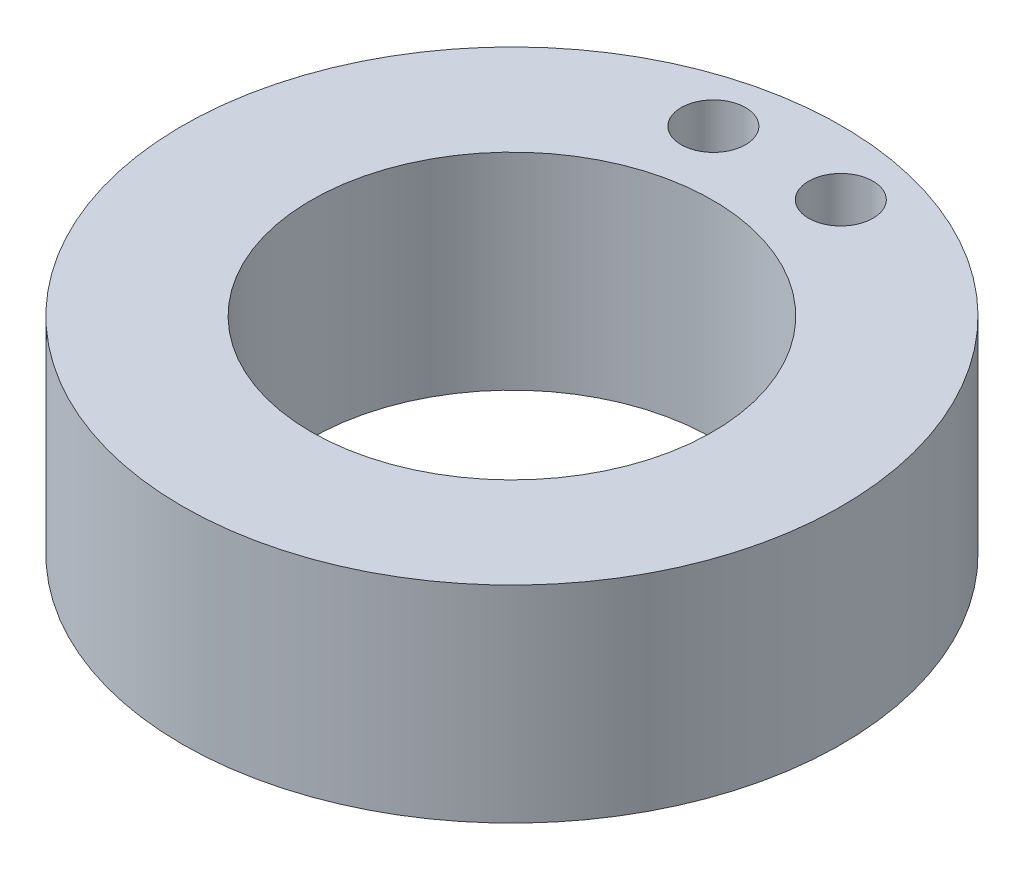
SolidWorks part; units mm, degrees
ref_plane "Front Plane" through (0, 0, 0) normal (0, 0, 1) x (1, 0, 0)
ref_plane "Top Plane" through (0, 0, 0) normal (0, 1, 0) x (1, 0, 0)
ref_plane "Right Plane" through (0, 0, 0) normal (1, 0, 0) x (0, 0, -1)
sketch "Sketch1" plane through (0, 0, 0) normal (0, 1, 0) x (1, 0, 0)
  line L0 (0, 9.8933) -> (0, 16.2433)
  circle A0 centre (0, 0) radius 9.8933
  circle A1 centre (0, 0) radius 16.2433
extrude "Boss-Extrude1" add sketch "Sketch1" along normal blind 10.16
sketch "Sketch2" plane through (0, 10.16, 0) normal (0, 1, 0) x (1, 0, 0)
  line L0 (0, 13.0683) -> (-3.1403, 13.0683)
  line L2 (0, 9.8933) -> (0, 16.2433)
  circle A0 centre (0, 0) radius 16.2433 construction
  circle A1 centre (0, 0) radius 9.8933 construction
  circle A3 centre (-3.1403, 13.0683) radius 1.5875
  circle A4 centre (3.1403, 13.0683) radius 1.5875
  point P11 (-3.1403, 13.0683)
extrude "Cut-Extrude2" cut sketch "Sketch2" against normal through all
